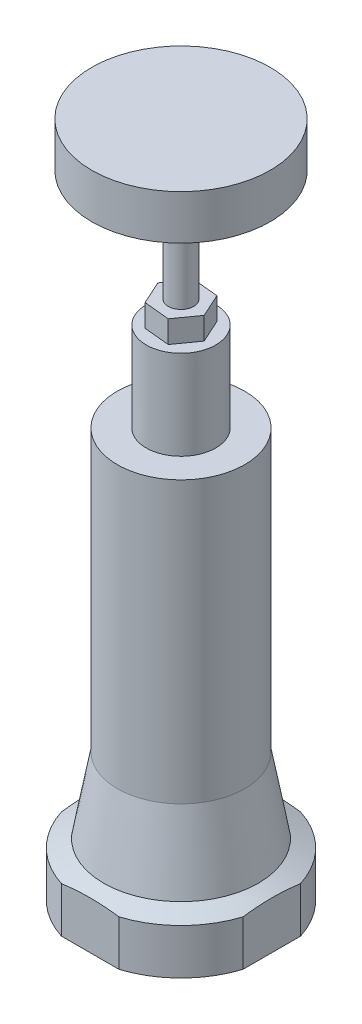
SolidWorks part; units mm, degrees
ref_plane "Front Plane" through (0, 0, 0) normal (0, 0, 1) x (1, 0, 0)
ref_plane "Top Plane" through (0, 0, 0) normal (0, 1, 0) x (1, 0, 0)
ref_plane "Right Plane" through (0, 0, 0) normal (1, 0, 0) x (0, 0, -1)
sketch "Sketch1" plane through (0, 0, 0) normal (0, 0, 1) x (1, 0, 0)
  line L0 (0, 0) -> (-18.1356, 0)
  line L1 (-18.1356, 0) -> (-18.1356, -79.883)
  line L2 (-18.1356, -79.883) -> (-22.0345, -101.219)
  line L3 (-22.0345, -101.219) -> (-27.1145, -103.505)
  line L4 (-27.1145, -103.505) -> (-27.1145, -116.459)
  line L5 (-27.1145, -116.459) -> (0, -116.459)
  line L6 (0, -116.459) -> (0, 0)
  dimension "D1" = 18.1356
  dimension "D2" = 27.1145
  dimension "D3" = 79.883
  dimension "D4" = 116.459
  dimension "D5" = 12.954
  dimension "D6" = 2.286
  dimension "D7" = 5.08
revolve "Revolve1" add sketch "Sketch1" angle 360 about L6
sketch "Sketch2" plane through (0, -116.459, 0) normal (0, -1, 0) x (1, 0, 0)
  line L1 (-25.8445, -25.8445) -> (25.8445, -25.8445)
  line L2 (-25.8445, -25.8445) -> (-25.8445, 25.8445)
  line L3 (-25.8445, 25.8445) -> (25.8445, 25.8445)
  line L4 (25.8445, -25.8445) -> (25.8445, 25.8445)
  line L5 (-25.8445, -25.8445) -> (25.8445, 25.8445) construction
  line L6 (-25.8445, 25.8445) -> (25.8445, -25.8445) construction
  point P0 (0, 0)
  dimension "D1" = 51.689
extrude "Extrude1" cut sketch "Sketch2" against normal blind 17.78 flip side to cut
sketch "Sketch3" plane through (0, 0, 0) normal (0, 1, 0) x (1, 0, 0)
  circle A0 centre (0, 0) radius 9.906
  dimension "D1" = 19.812
extrude "Extrude2" add sketch "Sketch3" along normal blind 25.4
sketch "Sketch4" plane through (0, 25.4, 0) normal (0, 1, 0) x (1, 0, 0)
  line L1 (-4.2655, -5.964) -> (3.0322, -6.676)
  line L2 (3.0322, -6.676) -> (7.2977, -0.712)
  line L3 (7.2977, -0.712) -> (4.2655, 5.964)
  line L4 (4.2655, 5.964) -> (-3.0322, 6.676)
  line L5 (-3.0322, 6.676) -> (-7.2977, 0.712)
  line L6 (-7.2977, 0.712) -> (-4.2655, -5.964)
  circle A0 centre (0, 0) radius 6.35 construction
  dimension "D1" = 12.7
extrude "Extrude3" add sketch "Sketch4" along normal blind 6.35
sketch "Sketch5" plane through (0, 31.75, 0) normal (0, 1, 0) x (1, 0, 0)
  circle A0 centre (0, 0) radius 3.6195
  dimension "D1" = 7.239
extrude "Extrude4" cut sketch "Sketch5" against normal blind 12.7
sketch "Sketch6" plane through (0, 31.75, 0) normal (0, 1, 0) x (1, 0, 0)
  circle A0 centre (0, 0) radius 3.6195
extrude "Extrude5" add sketch "Sketch6" along normal blind 31.75 separate body
sketch "Sketch7" plane through (0, 63.5, 0) normal (0, 1, 0) x (1, 0, 0)
  circle A0 centre (0, 0) radius 25.4
  dimension "D1" = 50.8
extrude "Extrude6" add sketch "Sketch7" along normal blind 12.7
